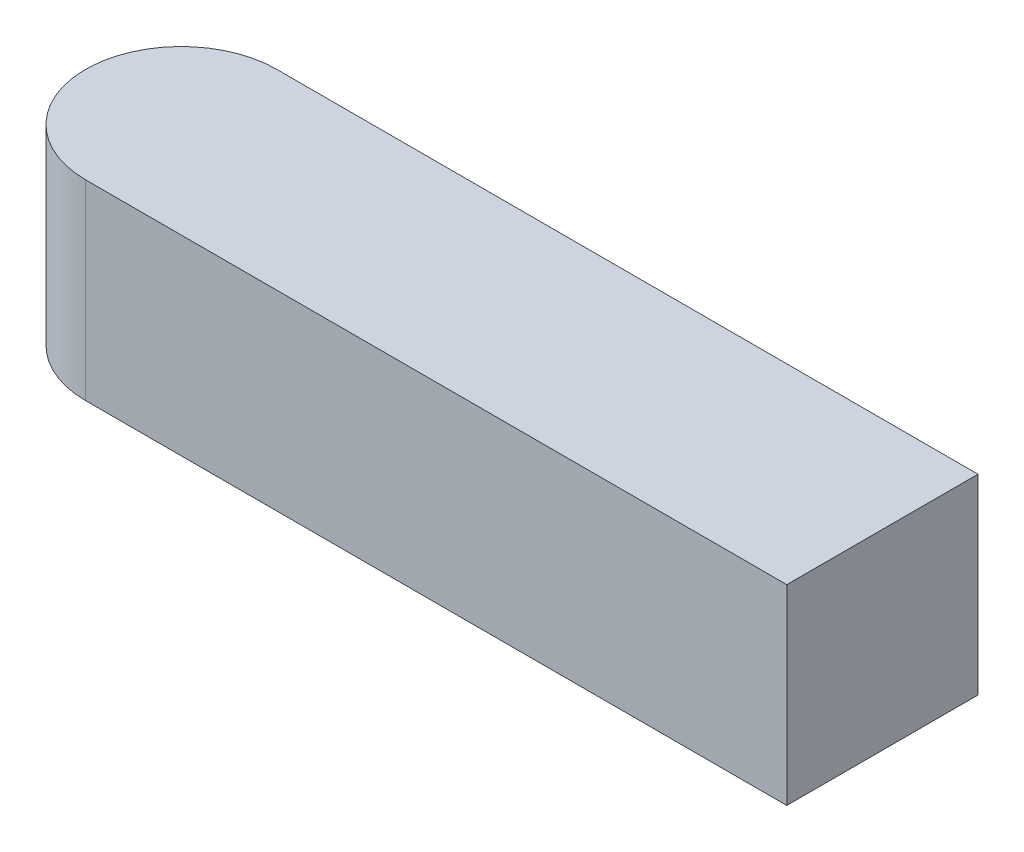
SolidWorks part; units mm, degrees
ref_plane "Front Plane" through (0, 0, 0) normal (0, 0, 1) x (1, 0, 0)
ref_plane "Top Plane" through (0, 0, 0) normal (0, 1, 0) x (1, 0, 0)
ref_plane "Right Plane" through (0, 0, 0) normal (1, 0, 0) x (0, 0, -1)
sketch "Sketch1" plane through (0, 0, 0) normal (0, 1, 0) x (1, 0, 0)
  line L0 (-50, 0) -> (50, 0) construction
  line L1 (-44, 0) -> (44, 0) construction
  line L2 (-44, 6) -> (44, 6)
  line L3 (-44, -6) -> (44, -6)
  arc A0 (-44, 6) -> (-44, -6) centre (-44, 0) ccw
  arc A1 (44, -6) -> (44, 6) centre (44, 0) ccw
  point P4 (0, 0)
  point P7 (0, 0)
  point P12 (0, 0)
  point P13 (0, 0)
  point P14 (0, 0)
  point P15 (0, 0)
  dimension "D" = 6
  dimension "L" = 100
extrude "Boss-Extrude1" add sketch "Sketch1" along normal blind 12
sketch "Sketch2" plane through (0, 12, 0) normal (0, 1, 0) x (1, 0, 0)
  line L0 (44, 6) -> (-44, 6) construction
  line L1 (0, 6) -> (50, 6)
  line L2 (0, 6) -> (0, -6)
  line L3 (0, -6) -> (50, -6)
  line L4 (50, 6) -> (50, -6)
  line L5 (-44, -6) -> (44, -6) construction
  arc A0 (44, -6) -> (44, 6) centre (44, 0) ccw construction
  point P6 (0, 0)
extrude "Cut-Extrude1" cut sketch "Sketch2" against normal through all
equation "\"L\" = 100"
equation "\"D\" = 6"
equation "\"H\"= 12"
equation "\"Cut-Extrude1\"= IIF ( \"L\" = 160 , \"unsuppressed\" , IIF ( \"L\" = 100 , \"unsuppressed\" , \"suppressed\" ) )"
equation "\"L@Sketch1\"=\"L\""
equation "\"D@Sketch1\"=\"D\""
equation "\"H@Boss-Extrude1\"=\"H\""
